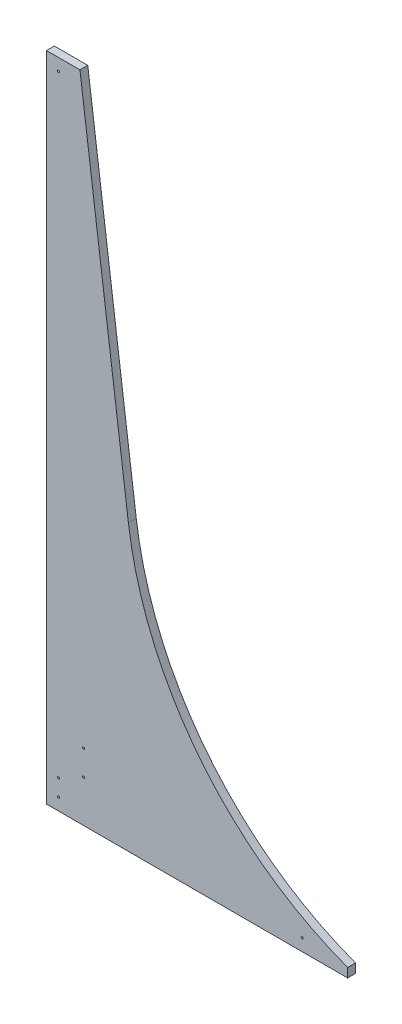
SolidWorks part; units mm, degrees
material "Pine"
ref_plane "Front Plane" through (0, 0, 0) normal (0, 0, 1) x (1, 0, 0)
ref_plane "Top Plane" through (0, 0, 0) normal (0, 1, 0) x (1, 0, 0)
ref_plane "Right Plane" through (0, 0, 0) normal (1, 0, 0) x (0, 0, -1)
sketch "Sketch1" plane through (0, 0, 0) normal (0, 0, 1) x (1, 0, 0)
  line L0 (0, 0) -> (500, 0)
  line L1 (0, 0) -> (0, 990.6)
  line L3 (0, 990.6) -> (50.8, 990.6)
  line L4 (50.8, 990.6) -> (124.3674, 431.8)
  line L7 (457.201, 13.862) -> (457.201, 0)
  circle A1 centre (18.2562, 18.2562) radius 1.5875
  circle A2 centre (388.1438, 18.2562) radius 1.5875
  circle A3 centre (18.2562, 972.3438) radius 1.5875
  circle A4 centre (56.3562, 101.6) radius 1.5875
  circle A6 centre (18.2562, 43.6562) radius 1.5875
  circle A7 centre (56.3562, 63.5) radius 1.5875
  arc A9 (124.3674, 431.8) -> (500, 0) centre (638.1166, 499.4364) ccw
  dimension "D7" = 3.175
  dimension "D8" = 18.2562
  dimension "D10" = 18.2562
  dimension "D11" = 3.175
  dimension "D12" = 18.2562
  dimension "D14" = 3.175
  dimension "D15" = 25.4
  dimension "D16" = 18.2562
  dimension "D17" = 101.6
  dimension "D18" = 50.8
  dimension "D24" = 3.175
  dimension "D1" = 500
  dimension "D2" = 990.6
  dimension "D3" = 42.799
  dimension "D4" = 50.8
  dimension "D5" = 558.8
  dimension "D6" = 97.5
  dimension "D9" = 18.2562
  dimension "D13" = 18.2562
  dimension "D20" = 38.1
  dimension "D21" = 38.1
extrude "Boss-Extrude1" add sketch "Sketch1" along normal blind 11.9062 contours A9 L4 L3 L1 L0 L7 A7 A6 A4 A3 A2 A1
